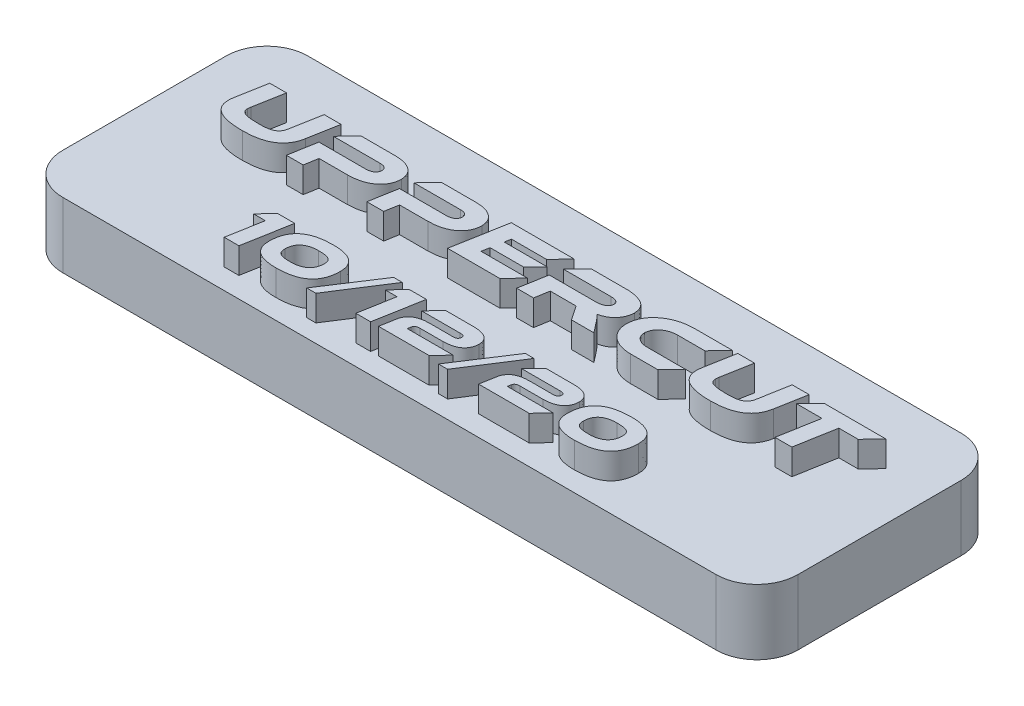
SolidWorks part; units mm, degrees
ref_plane "Front Plane" through (0, 0, 0) normal (0, 0, 1) x (1, 0, 0)
ref_plane "Top Plane" through (0, 0, 0) normal (0, 1, 0) x (1, 0, 0)
ref_plane "Right Plane" through (0, 0, 0) normal (1, 0, 0) x (0, 0, -1)
sketch "Sketch1" plane through (0, 0, 0) normal (0, 1, 0) x (1, 0, 0)
  line L1 (-28.575, 9.525) -> (28.575, 9.525)
  line L2 (-28.575, 9.525) -> (-28.575, -9.525)
  line L3 (-28.575, -9.525) -> (28.575, -9.525)
  line L4 (28.575, 9.525) -> (28.575, -9.525)
  line L5 (-28.575, 9.525) -> (28.575, -9.525) construction
  line L6 (-28.575, -9.525) -> (28.575, 9.525) construction
  point P0 (0, 0)
  dimension "D1" = 57.15
  dimension "D2" = 19.05
extrude "Boss-Extrude1" add sketch "Sketch1" along normal up to surface (5.08 mm away)
fillet "Fillet1" radius 3.175 4 edges at (-28.575, 2.54, 9.525) (-28.575, 2.54, -9.525) (28.575, 2.54, 9.525) (28.575, 2.54, -9.525)
sketch "Sketch3" plane through (0, 5.08, 0) normal (0, 1, 0) x (1, 0, 0)
  line L0 (28.575, -7.9375) -> (-28.575, -7.9375) construction
  line L1 (28.575, -6.35) -> (28.575, 6.35) construction
  line L2 (-28.575, 6.35) -> (-28.575, -6.35) construction
  line L3 (28.575, 0) -> (-28.575, 0) construction
  line L5 (-25.4, -9.525) -> (25.4, -9.525) construction
  line L6 (25.4, 9.525) -> (-25.4, 9.525) construction
  text T0 "Uppercut\r\n" font "Ethnocentric Rg" height in points 16
  text T1 "10/12/20\r\n" font "Ethnocentric Rg" height in points 14
  point P8 (-28.575, 0)
  dimension "D1" = 1.5875
extrude "Boss-Extrude2" add sketch "Sketch3" along normal blind 2
sketch "Sketch4" plane through (0, 0, 0) normal (0, -1, 0) x (1, 0, 0)
  line L0 (25.4, 0) -> (-25.4, 0) construction
  circle A0 centre (-25.4, 0) radius 0.9
  circle A1 centre (25.4, 0) radius 0.9
  point P3 (0, 0)
  dimension "D2" = 1.8
  dimension "D1" = 50.8
extrude "Cut-Extrude1" cut sketch "Sketch4" against normal blind 4
